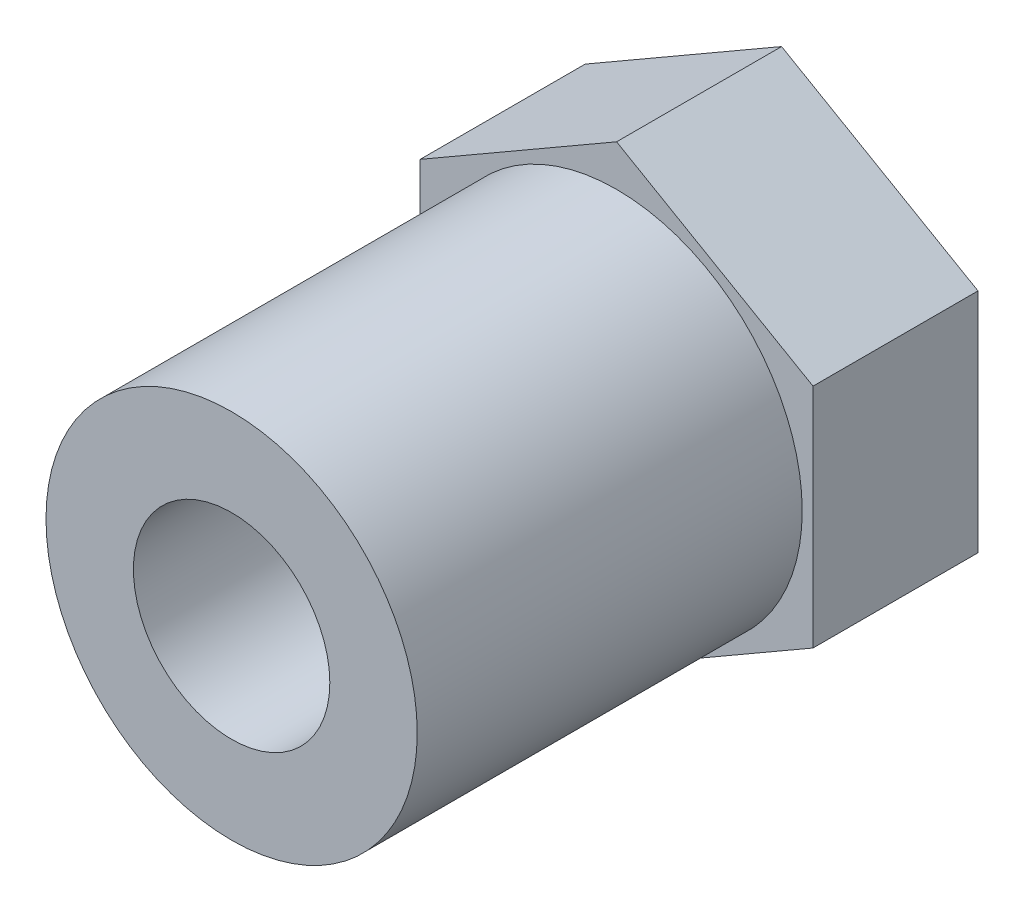
SolidWorks part; units mm, degrees
ref_plane "Front Plane" through (0, 0, 0) normal (0, 0, 1) x (1, 0, 0)
ref_plane "Top Plane" through (0, 0, 0) normal (0, 1, 0) x (1, 0, 0)
ref_plane "Right Plane" through (0, 0, 0) normal (1, 0, 0) x (0, 0, -1)
sketch "Sketch1" plane through (0, 0, 0) normal (0, 0, 1) x (1, 0, 0)
  line L1 (5, 2.8868) -> (0, 5.7735)
  line L2 (0, 5.7735) -> (-5, 2.8868)
  line L3 (-5, 2.8868) -> (-5, -2.8868)
  line L4 (-5, -2.8868) -> (0, -5.7735)
  line L5 (0, -5.7735) -> (5, -2.8868)
  line L6 (5, -2.8868) -> (5, 2.8868)
  circle A0 centre (0, 0) radius 5 construction
  circle A1 centre (0, 0) radius 2.5
  dimension "D2" = 5
  dimension "D1" = 10
extrude "Boss-Extrude1" add sketch "Sketch1" along normal blind 4.2
sketch "Sketch2" plane through (0, 0, 4.2) normal (0, 0, 1) x (1, 0, 0)
  circle A0 centre (0, 0) radius 4.725
  circle A1 centre (0, 0) radius 2.5
  dimension "D1" = 9.45
  dimension "D2" = 5
extrude "Boss-Extrude2" add sketch "Sketch2" along normal blind 9.8
